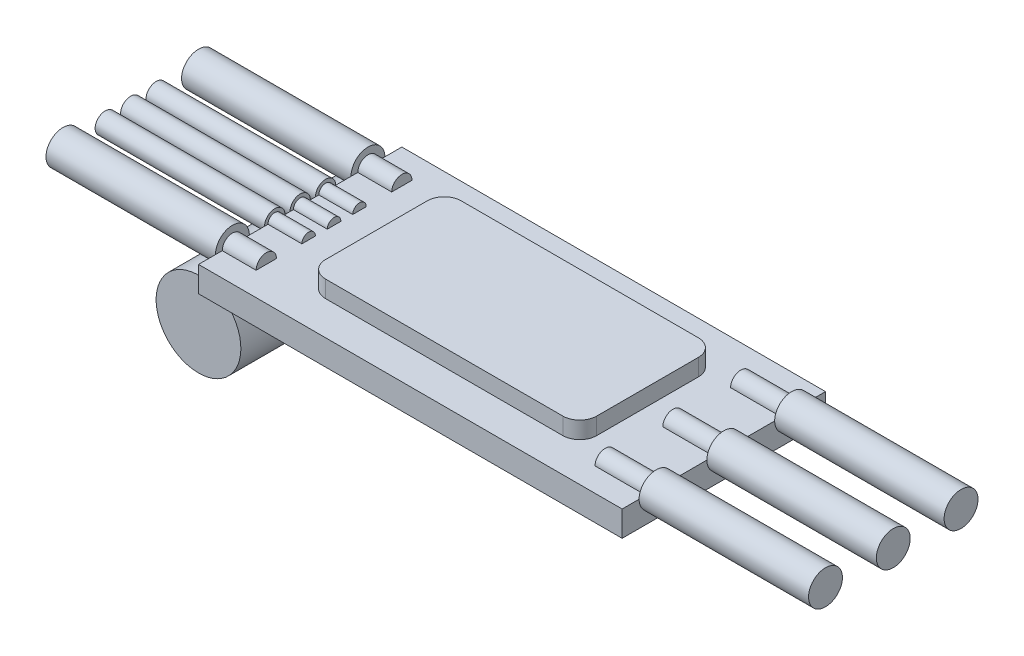
SolidWorks part; units mm, degrees
ref_plane "Front Plane" through (0, 0, 0) normal (0, 0, 1) x (1, 0, 0)
ref_plane "Top Plane" through (0, 0, 0) normal (0, 1, 0) x (1, 0, 0)
ref_plane "Right Plane" through (0, 0, 0) normal (1, 0, 0) x (0, 0, -1)
sketch "Sketch1" plane through (0, 0, 0) normal (0, 1, 0) x (1, 0, 0)
  line L1 (-12.5, -6) -> (12.5, -6)
  line L2 (-12.5, -6) -> (-12.5, 6)
  line L3 (-12.5, 6) -> (12.5, 6)
  line L4 (12.5, -6) -> (12.5, 6)
  line L5 (-12.5, -6) -> (12.5, 6) construction
  line L6 (-12.5, 6) -> (12.5, -6) construction
  point P0 (0, 0)
  dimension "D1" = 25
  dimension "D2" = 12
extrude "Boss-Extrude1" add sketch "Sketch1" along normal blind 1.5
sketch "Sketch2" plane through (12.5, 0, 0) normal (1, 0, 0) x (0, 0, -1)
  line L0 (-6, 1.5) -> (6, 1.5) construction
  circle A0 centre (0, 1.5) radius 1
  circle A1 centre (-4, 1.5) radius 1
  circle A2 centre (4, 1.5) radius 1
  dimension "D1" = 2
  dimension "D3" = 4
  dimension "D2" = 4
extrude "Boss-Extrude2" add sketch "Sketch2" along normal blind 10
sketch "Sketch3" plane through (12.5, 0, 0) normal (1, 0, 0) x (0, 0, -1)
  circle A0 centre (-4, 1.5) radius 0.6
  circle A1 centre (0, 1.5) radius 0.6
  circle A2 centre (4, 1.5) radius 0.6
  dimension "D1" = 1.2
extrude "Boss-Extrude3" add sketch "Sketch3" against normal blind 3
sketch "Sketch4" plane through (-12.5, 0, 0) normal (-1, 0, 0) x (0, 0, 1)
  line L0 (-4.6, 1.5) -> (-3.4, 1.5) construction
  line L1 (3.4, 1.5) -> (4.6, 1.5) construction
  line L2 (-0.6, 1.5) -> (0.6, 1.5) construction
  line L3 (-6, 1.5) -> (6, 1.5) construction
  circle A0 centre (-4, 1.5) radius 1
  circle A1 centre (4, 1.5) radius 1
  circle A2 centre (0, 1.5) radius 0.6
  circle A3 centre (1.5, 1.5) radius 0.6
  circle A4 centre (-1.5, 1.5) radius 0.6
  dimension "D1" = 1.2
  dimension "D2" = 1.5
  dimension "D3" = 1.5
extrude "Boss-Extrude4" add sketch "Sketch4" along normal blind 10
sketch "Sketch5" plane through (-12.5, 0, 0) normal (1, 0, 0) x (0, 0, -1)
  line L0 (-0.9, 1.5) -> (-2.1, 1.5) construction
  line L1 (2.1, 1.5) -> (0.9, 1.5) construction
  circle A0 centre (-4, 1.5) radius 0.6
  circle A1 centre (-1.5, 1.5) radius 0.4
  circle A2 centre (0, 1.5) radius 0.4
  circle A3 centre (1.5, 1.5) radius 0.4
  circle A4 centre (4, 1.5) radius 0.6
  dimension "D1" = 1.2
  dimension "D2" = 0.8
extrude "Boss-Extrude5" add sketch "Sketch5" along normal blind 2
sketch "Sketch6" plane through (0, 1.5, 0) normal (0, 1, 0) x (1, 0, 0)
  line L1 (-7, -4) -> (7, -4)
  line L2 (-8, -3) -> (-8, 3)
  line L3 (-7, 4) -> (7, 4)
  line L4 (8, -3) -> (8, 3)
  line L5 (-8, -4) -> (8, 4) construction
  line L6 (-8, 4) -> (8, -4) construction
  arc A0 (7, 4) -> (8, 3) centre (7, 3) cw
  arc A1 (8, -3) -> (7, -4) centre (7, -3) cw
  arc A2 (-7, -4) -> (-8, -3) centre (-7, -3) cw
  arc A3 (-7, 4) -> (-8, 3) centre (-7, 3) ccw
  point P0 (0, 0)
  dimension "D3" = 1
  dimension "D1" = 8
  dimension "D2" = 16
extrude "Boss-Extrude6" add sketch "Sketch6" along normal blind 1
ref_plane "Plane1" through (0, 0, 5.5) normal (0, 0, 1) x (1, 0, 0)
sketch "Sketch8" plane through (0, 0, 5.5) normal (0, 0, 1) x (1, 0, 0)
  circle A0 centre (-13, -2.05) radius 2.5
  dimension "D1" = 5
  dimension "D2" = 2.05
  dimension "D3" = 13
extrude "Boss-Extrude10" add sketch "Sketch8" against normal blind 11
sketch "Sketch9" plane through (0, 0, 0) normal (0, -1, 0) x (1, 0, 0)
  line L1 (-3.1812, -2.6351) -> (3.1812, -2.6351)
  line L2 (-3.1812, -2.6351) -> (-3.1812, 2.6351)
  line L3 (-3.1812, 2.6351) -> (3.1812, 2.6351)
  line L4 (3.1812, -2.6351) -> (3.1812, 2.6351)
  line L5 (-3.1812, -2.6351) -> (3.1812, 2.6351) construction
  line L6 (-3.1812, 2.6351) -> (3.1812, -2.6351) construction
  point P0 (0, 0)
extrude "Boss-Extrude11" add sketch "Sketch9" along normal blind 1
sketch "Sketch10" plane through (0, 0, 0) normal (0, -1, 0) x (1, 0, 0)
  line L1 (-9.6385, 2.6826) -> (-7.7393, 2.6826)
  line L2 (-9.6385, 2.6826) -> (-9.6385, 4.0121)
  line L3 (-9.6385, 4.0121) -> (-7.7393, 4.0121)
  line L4 (-7.7393, 2.6826) -> (-7.7393, 4.0121)
  line L5 (-9.6385, 2.6826) -> (-7.7393, 4.0121) construction
  line L6 (-9.6385, 4.0121) -> (-7.7393, 2.6826) construction
  line L7 (-8.2141, -2.9675) -> (-6.5997, -2.9675)
  line L8 (-8.2141, -2.9675) -> (-8.2141, -0.5935)
  line L9 (-8.2141, -0.5935) -> (-6.5997, -0.5935)
  line L10 (-6.5997, -2.9675) -> (-6.5997, -0.5935)
  line L11 (-8.2141, -2.9675) -> (-6.5997, -0.5935) construction
  line L12 (-8.2141, -0.5935) -> (-6.5997, -2.9675) construction
  line L13 (-0.2374, -4.3444) -> (3.1812, -4.3444)
  line L14 (-0.2374, -4.3444) -> (-0.2374, -3.4898)
  line L15 (-0.2374, -3.4898) -> (3.1812, -3.4898)
  line L16 (3.1812, -4.3444) -> (3.1812, -3.4898)
  line L17 (-0.2374, -4.3444) -> (3.1812, -3.4898) construction
  line L18 (-0.2374, -3.4898) -> (3.1812, -4.3444) construction
  line L19 (3.8459, -2.9675) -> (4.9854, -2.9675)
  line L20 (3.8459, -2.9675) -> (3.8459, -0.5935)
  line L21 (3.8459, -0.5935) -> (4.9854, -0.5935)
  line L22 (4.9854, -2.9675) -> (4.9854, -0.5935)
  line L23 (3.8459, -2.9675) -> (4.9854, -0.5935) construction
  line L24 (3.8459, -0.5935) -> (4.9854, -2.9675) construction
  line L25 (5.2703, 3.1099) -> (6.5048, 3.1099)
  line L26 (5.2703, 3.1099) -> (5.2703, 4.9142)
  line L27 (5.2703, 4.9142) -> (6.5048, 4.9142)
  line L28 (6.5048, 3.1099) -> (6.5048, 4.9142)
  line L29 (5.2703, 3.1099) -> (6.5048, 4.9142) construction
  line L30 (5.2703, 4.9142) -> (6.5048, 3.1099) construction
  line L31 (7.1476, 3.1099) -> (8.4989, 3.1099)
  line L32 (7.1476, 3.1099) -> (7.1476, 4.9142)
  line L33 (7.1476, 4.9142) -> (8.4989, 4.9142)
  line L34 (8.4989, 3.1099) -> (8.4989, 4.9142)
  line L35 (7.1476, 3.1099) -> (8.4989, 4.9142) construction
  line L36 (7.1476, 4.9142) -> (8.4989, 3.1099) construction
  line L37 (6.198, 0.5935) -> (9.4485, 0.5935)
  line L38 (6.198, 0.5935) -> (6.198, -0.5935)
  line L39 (6.198, -0.5935) -> (9.4485, -0.5935)
  line L40 (9.4485, 0.5935) -> (9.4485, -0.5935)
  line L41 (6.198, 0.5935) -> (9.4485, -0.5935) construction
  line L42 (6.198, -0.5935) -> (9.4485, 0.5935) construction
  point P0 (-8.6889, 3.3473)
  point P5 (-7.4069, -1.7805)
  point P10 (1.4719, -3.9171)
  point P15 (4.4156, -1.7805)
  point P20 (5.8875, 4.0121)
  point P25 (7.8233, 4.0121)
  point P30 (7.8233, 0)
extrude "Boss-Extrude12" add sketch "Sketch10" along normal blind 0.8
